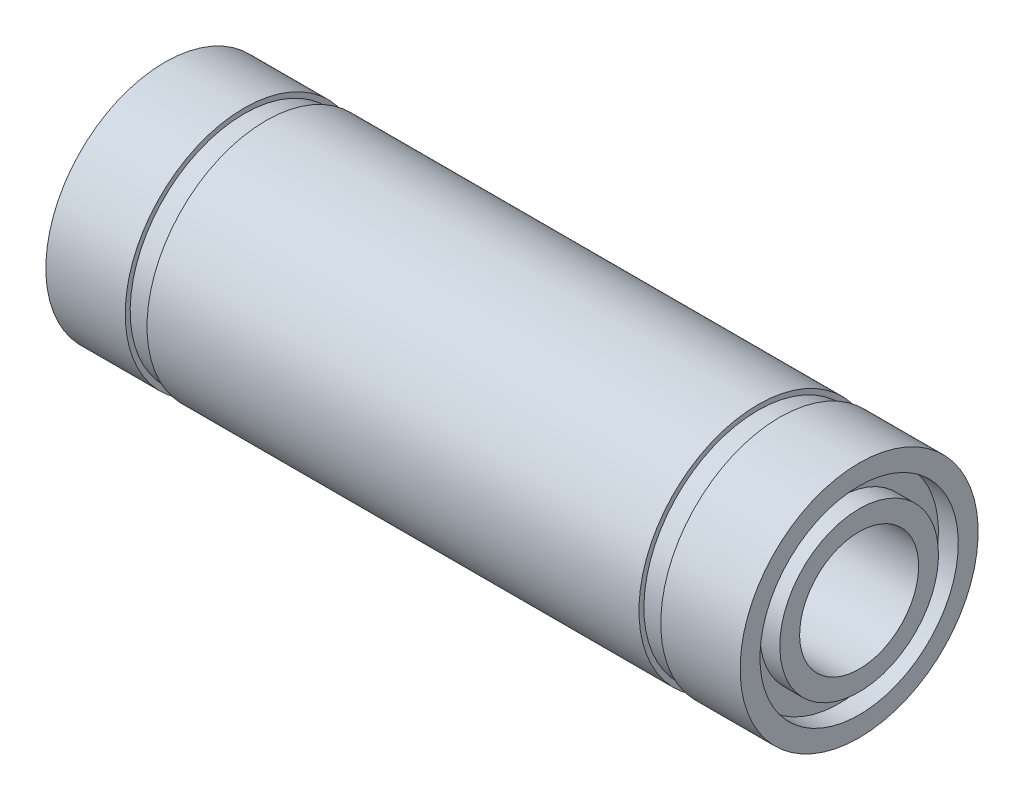
SolidWorks part; units mm, degrees
material "Ст3сп ГОСТ 535-2005"
ref_plane "Plano frontal" through (0, 0, 0) normal (0, 0, 1) x (1, 0, 0)
ref_plane "Plano superior" through (0, 0, 0) normal (0, 1, 0) x (1, 0, 0)
ref_plane "Plano direito" through (0, 0, 0) normal (1, 0, 0) x (0, 0, -1)
sketch "Esboço1" plane through (0, 0, 0) normal (0, 0, 1) x (1, 0, 0)
  line L0 (-17.5, 6) -> (-13.5, 6)
  line L1 (-13.5, 6) -> (-13.5, 5.75)
  line L2 (-13.5, 5.75) -> (-12.4, 5.75)
  line L3 (-12.4, 5.75) -> (-12.4, 6)
  line L4 (-12.4, 6) -> (12.4, 6)
  line L5 (12.4, 6) -> (12.4, 5.75)
  line L6 (12.4, 5.75) -> (13.5, 5.75)
  line L7 (13.5, 5.75) -> (13.5, 6)
  line L8 (13.5, 6) -> (17.5, 6)
  line L9 (17.5, 6) -> (17.5, 5)
  line L10 (17.5, 3) -> (-17.5, 3)
  line L11 (-17.5, 3) -> (-17.5, 4)
  line L12 (0, 3) -> (0, 0) construction
  line L13 (0, 0) -> (-86.5, 0) construction
  line L14 (-17.5, 5) -> (-17.5, 6)
  line L15 (-17.5, 5) -> (-16.5, 5)
  line L16 (17.5, 4) -> (17.5, 3)
  line L17 (-16.5, 5) -> (-16.5, 4)
  line L18 (-16.5, 4) -> (-17.5, 4)
  line L19 (17.5, 5) -> (16.5, 5)
  line L21 (17.5, 4) -> (16.5, 4)
  line L22 (16.5, 5) -> (16.5, 4)
  dimension "D1" = 35
  dimension "D2" = 27
  dimension "D3" = 1.1
  dimension "D4" = 6
  dimension "D5" = 12
  dimension "D6" = 11.5
  dimension "D7" = 1
  dimension "D8" = 1
  dimension "D9" = 1
  dimension "D10" = 1
revolve "Revolução1" add sketch "Esboço1" angle 360 about L13
